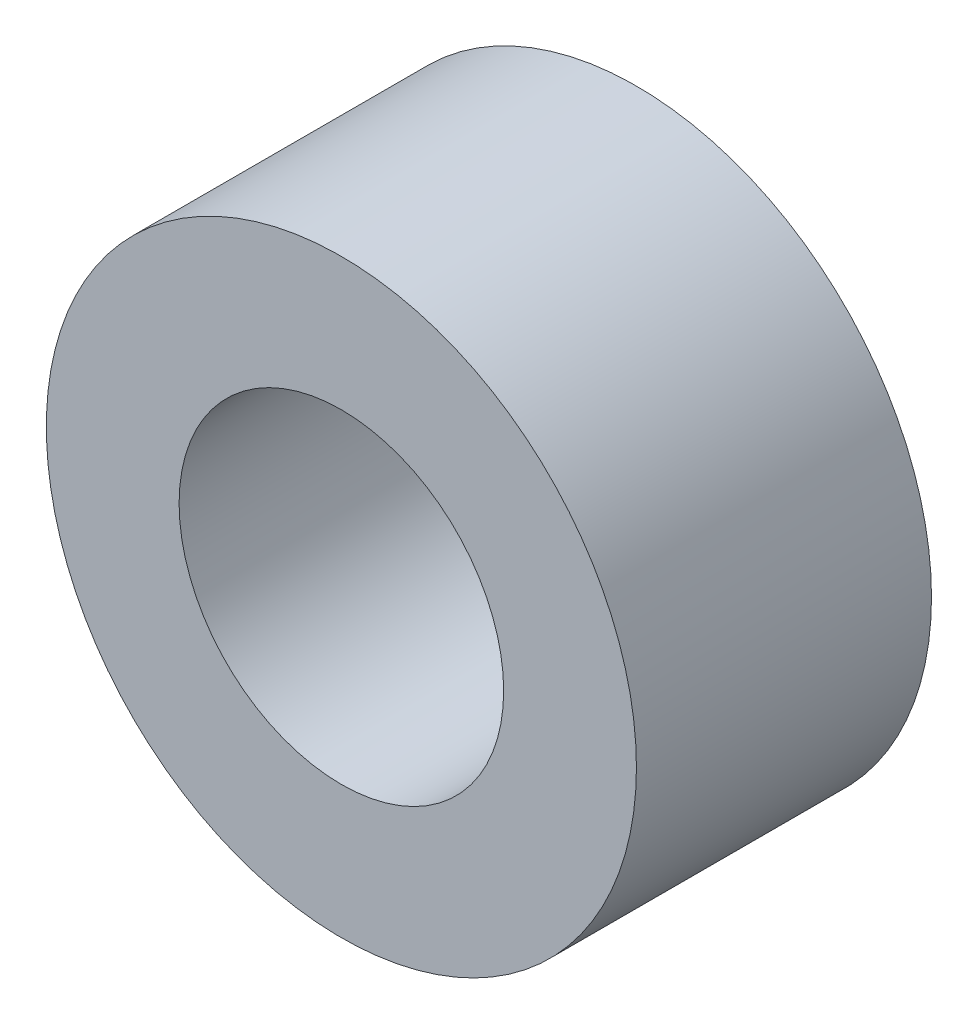
SolidWorks part; units mm, degrees
ref_plane "Plan de face" through (0, 0, 0) normal (0, 0, 1) x (1, 0, 0)
ref_plane "Plan de dessus" through (0, 0, 0) normal (0, 1, 0) x (1, 0, 0)
ref_plane "Plan de droite" through (0, 0, 0) normal (1, 0, 0) x (0, 0, -1)
sketch "Esquisse1" plane through (0, 0, 0) normal (0, 0, 1) x (1, 0, 0)
  circle A0 centre (0, 0) radius 1.1
  circle A1 centre (0, 0) radius 2
  dimension "D1" = 4
  dimension "D2" = 2.2
extrude "Boss.-Extru.1" add sketch "Esquisse1" along normal blind 2
